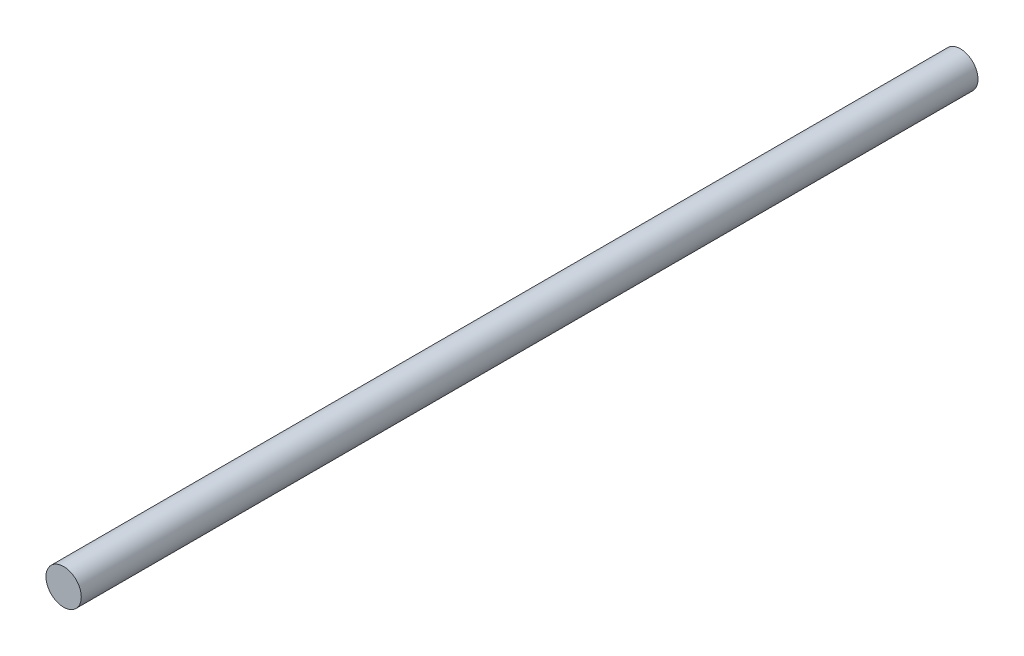
SolidWorks part; units mm, degrees
ref_plane "Front Plane" through (0, 0, 0) normal (0, 0, 1) x (1, 0, 0)
ref_plane "Top Plane" through (0, 0, 0) normal (0, 1, 0) x (1, 0, 0)
ref_plane "Right Plane" through (0, 0, 0) normal (1, 0, 0) x (0, 0, -1)
sketch "Sketch1" plane through (0, 0, 0) normal (0, 0, 1) x (1, 0, 0)
  circle A0 centre (0, 0) radius 6.35
  dimension "D1" = 12.7
extrude "Boss-Extrude1" add sketch "Sketch1" along normal blind 322.58
